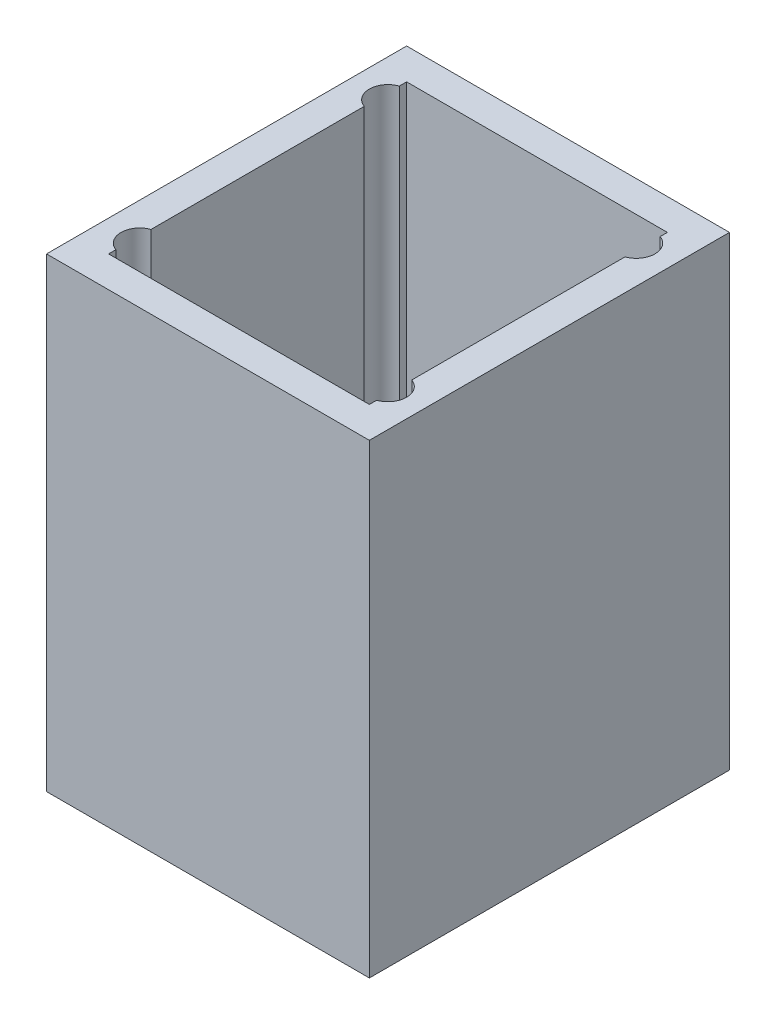
SolidWorks part; units mm, degrees
ref_plane "Front Plane" through (0, 0, 0) normal (0, 0, 1) x (1, 0, 0)
ref_plane "Top Plane" through (0, 0, 0) normal (0, 1, 0) x (1, 0, 0)
ref_plane "Right Plane" through (0, 0, 0) normal (1, 0, 0) x (0, 0, -1)
sketch "Sketch1" plane through (0, 0, 0) normal (0, 1, 0) x (1, 0, 0)
  line L0 (-55, 0) -> (55, 0) construction
  line L1 (-26, 29) -> (26, 29)
  line L2 (-26, 29) -> (-26, -29)
  line L3 (-26, -29) -> (26, -29)
  line L4 (26, 29) -> (26, -29)
  line L5 (-26, 29) -> (26, -29) construction
  line L6 (-26, -29) -> (26, 29) construction
  line L7 (0, -55) -> (0, 55) construction
  circle A0 centre (-20, 20) radius 1.7
  circle A1 centre (-20, -20) radius 1.7
  circle A2 centre (20, -20) radius 1.7
  circle A3 centre (20, 20) radius 1.7
  point P0 (0, 0)
  dimension "D3" = 3.4
  dimension "D6" = 3.4
  dimension "D1" = 52
  dimension "D2" = 58
  dimension "D4" = 20
  dimension "D5" = 20
  dimension "D7" = 20
  dimension "D8" = 20
extrude "Boss-Extrude1" add sketch "Sketch1" along normal blind 2
sketch "Sketch2" plane through (0, 2, 0) normal (0, 1, 0) x (1, 0, 0)
  line L1 (-26, -29) -> (26, -29)
  line L2 (-26, -29) -> (-26, 29)
  line L3 (-26, 29) -> (26, 29)
  line L4 (26, -29) -> (26, 29)
  line L5 (-26, -29) -> (26, 29) construction
  line L6 (-26, 29) -> (26, -29) construction
  circle A0 centre (-20, 20) radius 3
  circle A1 centre (-20, -20) radius 3
  circle A2 centre (20, 20) radius 3
  circle A3 centre (20, -20) radius 3
  point P0 (0, 0)
  dimension "D1" = 6
extrude "Boss-Extrude2" add sketch "Sketch2" along normal blind 3 contours L2 L1 L4 L3 | A0 | A1 | A3 | A2
sketch "Sketch3" plane through (0, 5, 0) normal (0, 1, 0) x (1, 0, 0)
  line L1 (-26, 29) -> (26, 29)
  line L2 (-26, 29) -> (-26, -29)
  line L3 (-26, -29) -> (26, -29)
  line L4 (26, 29) -> (26, -29)
  line L5 (-26, 29) -> (26, -29) construction
  line L6 (-26, -29) -> (26, 29) construction
  line L7 (-21, 24) -> (21, 24)
  line L8 (-21, 24) -> (-21, -24)
  line L9 (-21, -24) -> (21, -24)
  line L10 (21, 24) -> (21, -24)
  line L11 (-21, 24) -> (21, -24) construction
  line L12 (-21, -24) -> (21, 24) construction
  circle A0 centre (-20, 20) radius 3
  circle A1 centre (20, 20) radius 3
  circle A2 centre (20, -20) radius 3
  circle A3 centre (-20, -20) radius 3
  point P0 (0, 0)
  point P7 (0, 0)
  circle M9 centre (20, -20) radius 3
  circle M10 centre (-20, 20) radius 3
  line M11 (26, 29) -> (-26, 29)
  line M12 (-26, 29) -> (-26, -29)
  line M13 (-26, -29) -> (26, -29)
  line M14 (26, -29) -> (26, 29)
  circle M15 centre (-20, -20) radius 3
  circle M16 centre (20, 20) radius 3
  dimension "D1" = 5
  dimension "D2" = 5
extrude "Boss-Extrude3" add sketch "Sketch3" along normal blind 70 contours L7 L10 L9 L8 M14 M11 M12 M13 M16 M9 M15 M10
